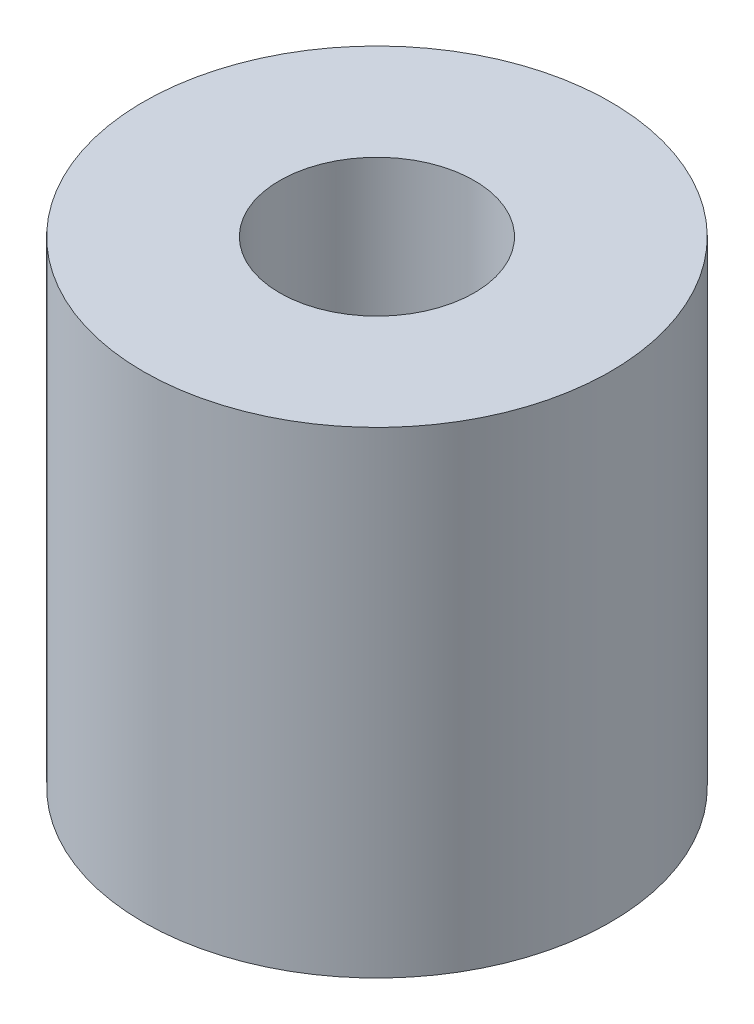
SolidWorks part; units mm, degrees
ref_plane "Front Plane" through (0, 0, 0) normal (0, 0, 1) x (1, 0, 0)
ref_plane "Top Plane" through (0, 0, 0) normal (0, 1, 0) x (1, 0, 0)
ref_plane "Right Plane" through (0, 0, 0) normal (1, 0, 0) x (0, 0, -1)
sketch "Sketch1" plane through (0, 0, 0) normal (0, 1, 0) x (1, 0, 0)
  circle A0 centre (0, 0) radius 48
  circle A1 centre (0, 0) radius 20
  dimension "D1" = 96
  dimension "D2" = 40
extrude "Boss-Extrude1" add sketch "Sketch1" along normal blind 98
